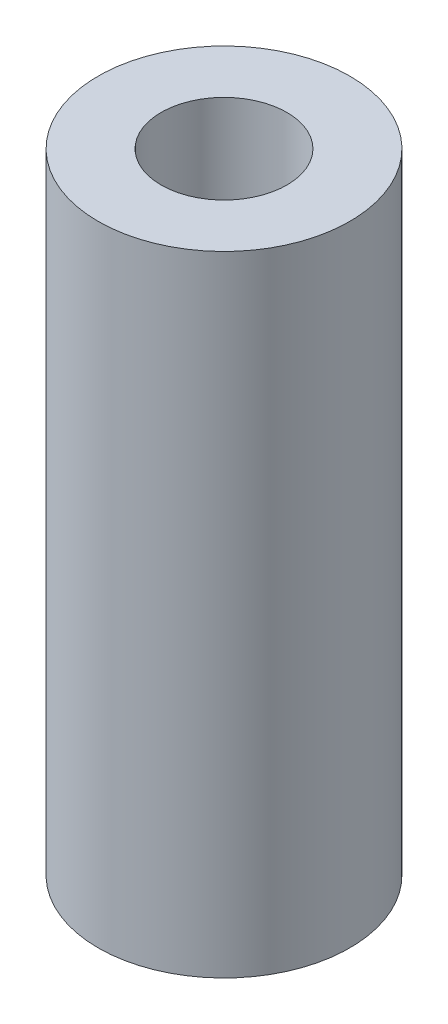
SolidWorks part; units mm, degrees
ref_plane "Front Plane" through (0, 0, 0) normal (0, 0, 1) x (1, 0, 0)
ref_plane "Top Plane" through (0, 0, 0) normal (0, 1, 0) x (1, 0, 0)
ref_plane "Right Plane" through (0, 0, 0) normal (1, 0, 0) x (0, 0, -1)
sketch "Sketch1" plane through (0, 0, 0) normal (0, 1, 0) x (1, 0, 0)
  circle A0 centre (0, 0) radius 2.5
  circle A1 centre (0, 0) radius 5
  dimension "D1" = 5
  dimension "D2" = 10
extrude "Boss-Extrude1" add sketch "Sketch1" along normal blind 25
